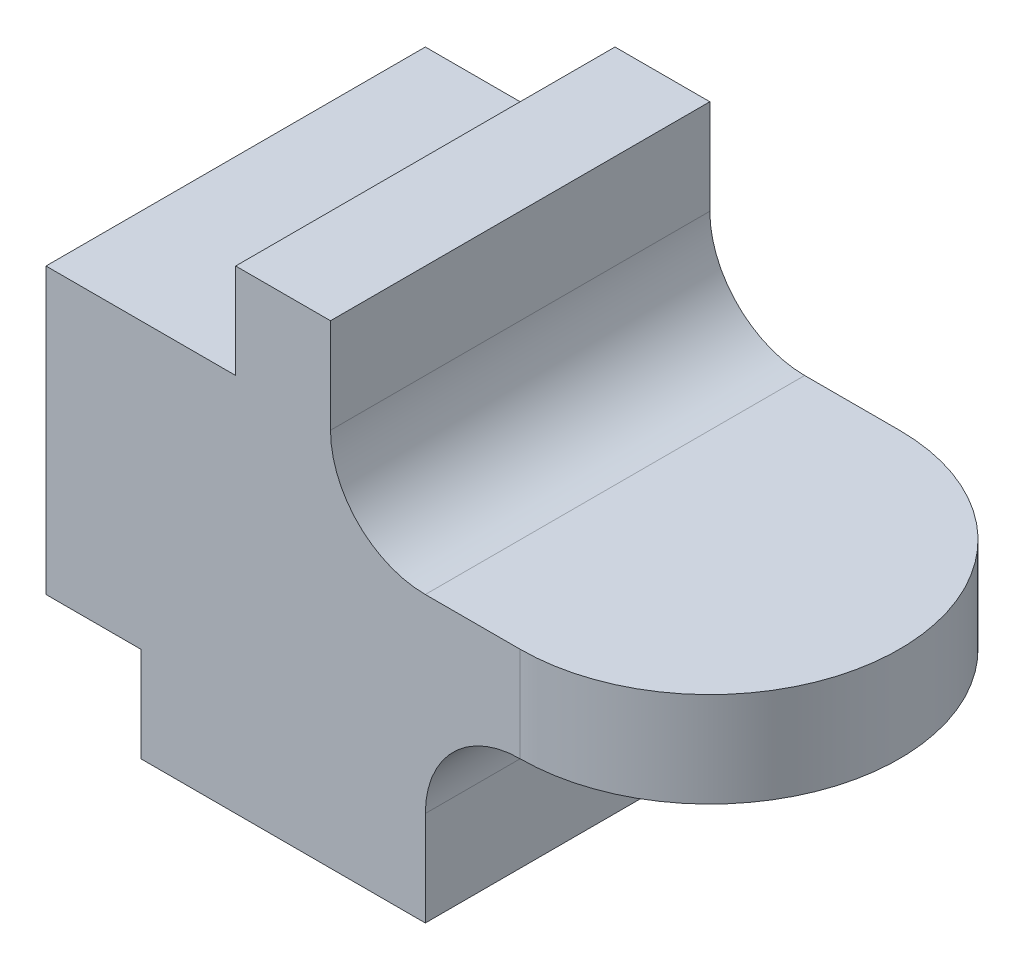
SolidWorks part; units mm, degrees
ref_plane "前基準面" through (0, 0, 0) normal (0, 0, 1) x (1, 0, 0)
ref_plane "上基準面" through (0, 0, 0) normal (0, 1, 0) x (1, 0, 0)
ref_plane "右基準面" through (0, 0, 0) normal (1, 0, 0) x (0, 0, -1)
sketch "草圖2" plane through (0, 0, 0) normal (0, 1, 0) x (1, 0, 0)
  line L1 (-35, -20) -> (35, -20)
  line L2 (-35, -20) -> (-35, 20)
  line L3 (-35, 20) -> (35, 20)
  line L4 (35, -20) -> (35, 20)
  line L5 (-35, -20) -> (35, 20) construction
  line L6 (-35, 20) -> (35, -20) construction
  point P0 (0, 0)
  dimension "D1" = 70
  dimension "D2" = 40
extrude "填料-伸長1" add sketch "草圖2" along normal blind 50
sketch "草圖3" plane through (0, 0, 20) normal (0, 0, 1) x (1, 0, 0)
  line L0 (35, 50) -> (35, 0) construction
  line L1 (-35, 0) -> (-25, 0)
  line L2 (-35, 0) -> (-35, 10)
  line L3 (-35, 10) -> (-25, 10)
  line L4 (-25, 0) -> (-25, 10)
  line L5 (-35, 50) -> (-15, 50)
  line L6 (-35, 50) -> (-35, 40)
  line L7 (-35, 40) -> (-15, 40)
  line L8 (-15, 50) -> (-15, 40)
  line L9 (35, 50) -> (-5, 50)
  line L10 (35, 50) -> (35, 30)
  line L11 (35, 30) -> (-5, 30)
  line L12 (-5, 50) -> (-5, 30)
  line L13 (-35, 50) -> (35, 50) construction
  line L15 (35, 0) -> (5, 0)
  line L16 (35, 0) -> (35, 20)
  line L17 (35, 20) -> (5, 20)
  line L18 (5, 0) -> (5, 20)
  arc A0 (-5, 40) -> (5, 30) centre (5, 40) ccw
  arc A1 (15, 20) -> (5, 10) centre (15, 10) ccw
  line M9 (-35, 0) -> (35, 0)
  line M10 (35, 0) -> (35, 50)
  line M11 (35, 50) -> (-35, 50)
  line M12 (-35, 50) -> (-35, 0)
  dimension "D9" = 10
  dimension "D1" = 10
  dimension "D2" = 20
  dimension "D3" = 10
  dimension "D4" = 10
  dimension "D5" = 20
  dimension "D6" = 20
  dimension "D7" = 10
  dimension "D8" = 30
extrude "除料-伸長1" cut sketch "草圖3" against normal through all contours L8 L7 M11 M12 | L12 A0 L11 M10 M11 | L17 A1 L18 M9 M10 | L4 L3 M9 M12
sketch "草圖4" plane through (0, 0, 0) normal (0, 1, 0) x (1, 0, 0)
  line L0 (35, 20) -> (35, -20) construction
  line L1 (35, 20) -> (5, 20) construction
  line L2 (35, -20) -> (5, -20) construction
  line L3 (15, 20) -> (35, 20)
  line L4 (35, 20) -> (35, -20)
  line L5 (35, -20) -> (15, -20)
  arc A0 (35, 0) -> (15, 20) centre (15, 0) ccw
  arc A1 (35, 0) -> (15, -20) centre (15, 0) cw
  dimension "D1" = 20
extrude "除料-伸長3" cut sketch "草圖4" against normal through all and the other way through all contours A0 L4 L3 | L4 A1 L5
